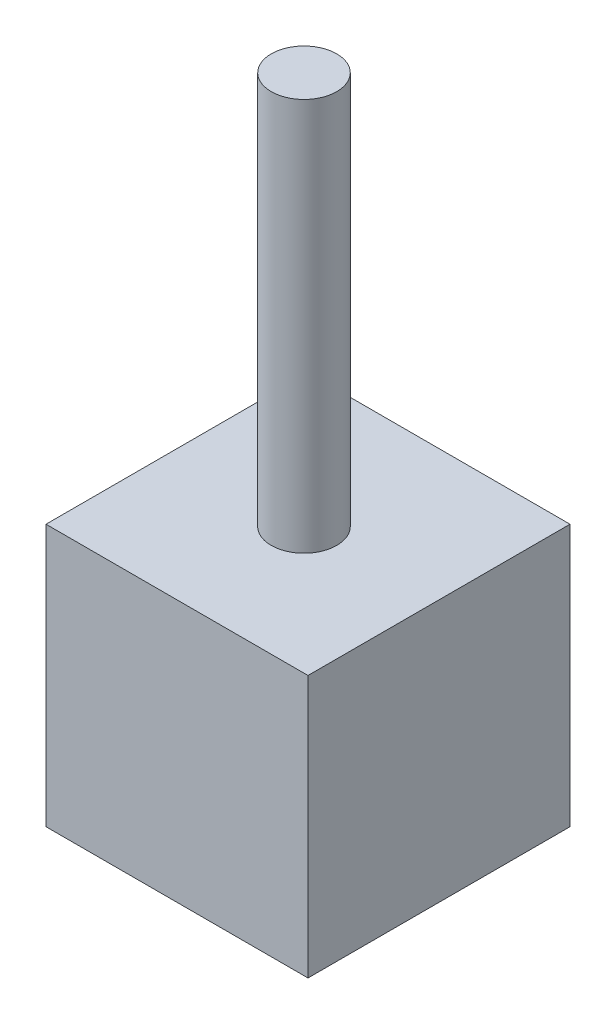
SolidWorks part; units mm, degrees
ref_plane "Front Plane" through (0, 0, 0) normal (0, 0, 1) x (1, 0, 0)
ref_plane "Top Plane" through (0, 0, 0) normal (0, 1, 0) x (1, 0, 0)
ref_plane "Right Plane" through (0, 0, 0) normal (1, 0, 0) x (0, 0, -1)
sketch "Sketch1" plane through (0, 0, 0) normal (0, 1, 0) x (1, 0, 0)
  line L1 (-25.4, -24.6202) -> (25.4, -24.6202)
  line L2 (-25.4, -24.6202) -> (-25.4, 26.1798)
  line L3 (-25.4, 26.1798) -> (25.4, 26.1798)
  line L4 (25.4, -24.6202) -> (25.4, 26.1798)
  point P4 (0, 26.1798)
  dimension "D1" = 50.8
  dimension "D2" = 50.8
extrude "Boss-Extrude1" add sketch "Sketch1" along normal blind 50.8
sketch "Sketch2" plane through (0, 50.8, 0) normal (0, 1, 0) x (1, 0, 0)
  circle A0 centre (0, 0) radius 6.35
  dimension "D1" = 12.7
extrude "Boss-Extrude2" add sketch "Sketch2" along normal blind 76.2
